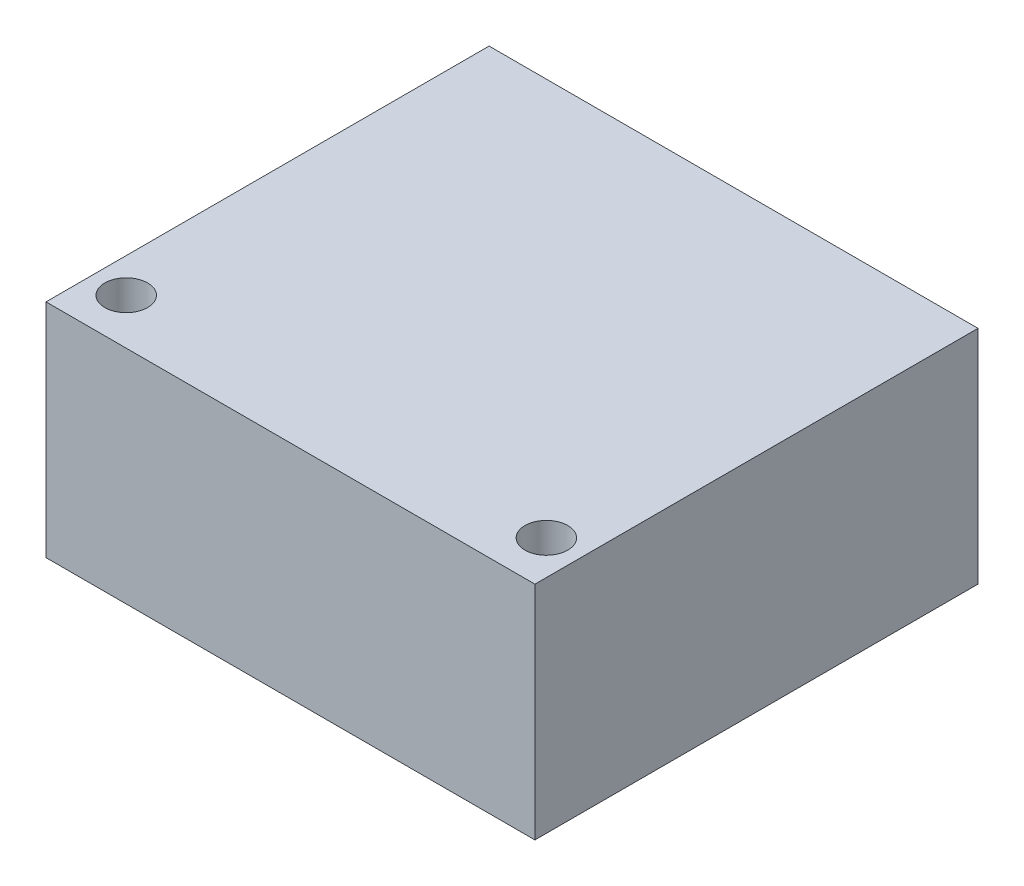
SolidWorks part; units mm, degrees
ref_plane "前视基准面" through (0, 0, 0) normal (0, 0, 1) x (1, 0, 0)
ref_plane "上视基准面" through (0, 0, 0) normal (0, 1, 0) x (1, 0, 0)
ref_plane "右视基准面" through (0, 0, 0) normal (1, 0, 0) x (0, 0, -1)
sketch "草图1" plane through (0, 0, 0) normal (0, 1, 0) x (1, 0, 0)
  line L1 (-16, 14.5) -> (16, 14.5)
  line L2 (-16, 14.5) -> (-16, -14.5)
  line L3 (-16, -14.5) -> (16, -14.5)
  line L4 (16, 14.5) -> (16, -14.5)
  line L5 (-16, 14.5) -> (16, -14.5) construction
  line L6 (-16, -14.5) -> (16, 14.5) construction
  point P0 (0, 0)
  dimension "D1" = 32
  dimension "D2" = 29
extrude "凸台-拉伸1" add sketch "草图1" along normal blind 14.5
sketch "草图2" plane through (0, 14.5, 0) normal (0, 1, 0) x (1, 0, 0)
  line L0 (-16, 14.5) -> (-16, -14.5) construction
  line L2 (16, 14.5) -> (-16, 14.5) construction
  circle A0 centre (-13.75, -11.5) radius 1.4
  circle A1 centre (13.75, -11.5) radius 1.4
  dimension "D2" = 2.8
  dimension "D1" = 27.5
  dimension "D3" = 2.25
  dimension "D4" = 26
extrude "切除-拉伸1" cut sketch "草图2" against normal through all
